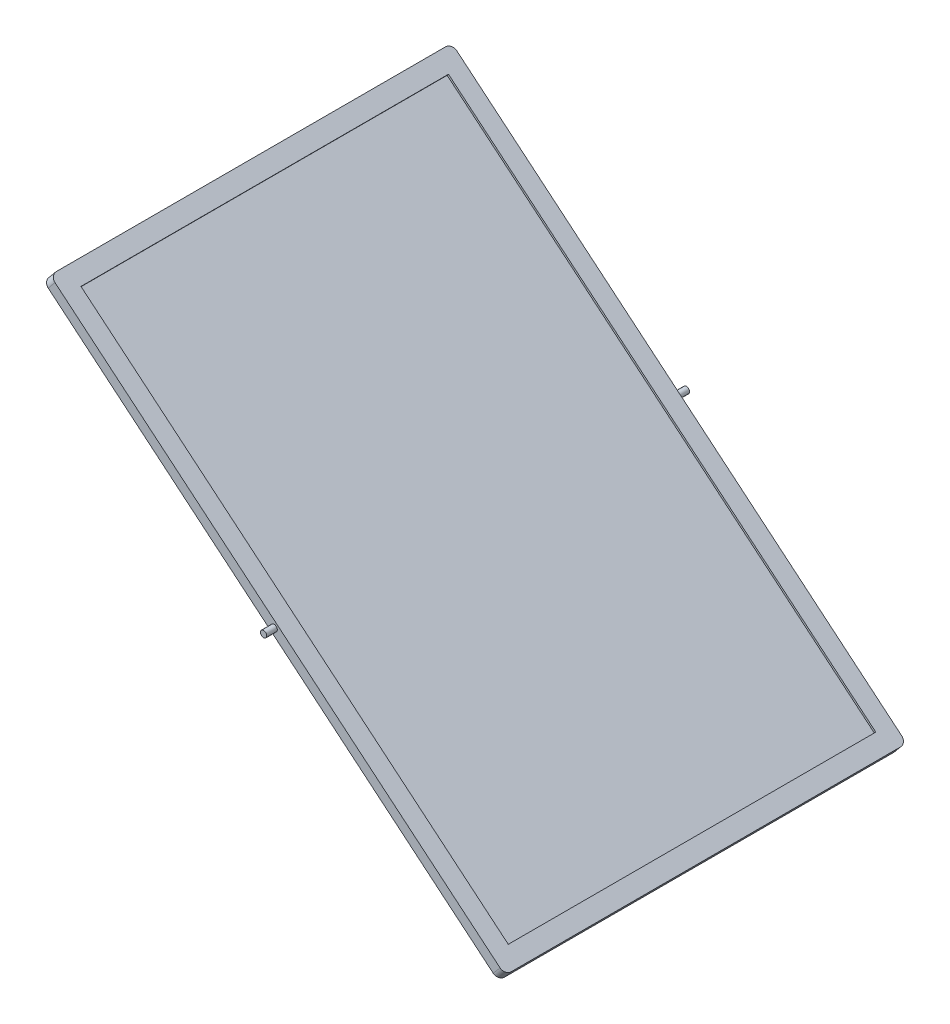
SolidWorks part; units mm, degrees
ref_plane "Front" through (0, 0, 0) normal (0, 0, 1) x (1, 0, 0)
ref_plane "Top" through (0, 0, 0) normal (0, 1, 0) x (1, 0, 0)
ref_plane "Right" through (0, 0, 0) normal (1, 0, 0) x (0, 0, -1)
sketch "草图1" plane through (0, 0, 0) normal (0, 0, 1) x (1, 0, 0)
  line L0 (-7.852, 22.5836) -> (-11.0529, 18.7425)
  line L1 (-11.0529, 18.7425) -> (204.049, -160.5092)
  line L2 (204.049, -160.5092) -> (207.25, -156.6681)
  line L3 (207.25, -156.6681) -> (-7.852, 22.5836)
  dimension "D1" = 5
  dimension "D2" = 280
extrude "凸台-拉伸1" add sketch "草图1" along normal blind 190
fillet "圆角1" radius 3 1 edges at (205.6495, -158.5886, 0)
fillet "圆角2" radius 3 1 edges at (205.6495, -158.5886, 190)
fillet "圆角3" radius 3 1 edges at (-9.4524, 20.663, 190)
fillet "圆角4" radius 3 1 edges at (-9.4524, 20.663, 0)
sketch "草图2" plane through (7.8887, 9.4664, 0) normal (0.6402, 0.7682, 0) x (0.7682, -0.6402, 0)
  line L0 (-43.7388, -95) -> (285.8015, -95) construction
  line L1 (-12.0278, -8.0871) -> (251.0484, -8.0871)
  line L2 (-12.0278, -8.0871) -> (-12.0278, -181.9129)
  line L3 (-12.0278, -181.9129) -> (251.0484, -181.9129)
  line L4 (251.0484, -8.0871) -> (251.0484, -181.9129)
  line L5 (256.5103, 0) -> (-17.4897, 0) construction
  line L6 (256.5103, -190) -> (-17.4897, -190) construction
  line L7 (119.5103, 26.5158) -> (119.5103, -214.3222) construction
  line L8 (259.5103, -187) -> (259.5103, -3) construction
  line L9 (-20.4897, -187) -> (-20.4897, -3) construction
extrude "切除-拉伸1" cut sketch "草图2" against normal blind 1
sketch "草图3" plane through (0, 0, 0) normal (0, 0, -1) x (-1, 0, 0)
  line L4 (-80.4882, -90.0952) -> (-128.8367, -32.077) construction
  line L5 (13.3016, 23.8707) -> (-215.8703, -167.1059) construction
  line L6 (8.7482, 16.8219) -> (-201.7444, -158.5886) construction
  line L7 (-204.9453, -154.7475) -> (5.5473, 20.663) construction
  line L8 (8.7482, 16.8219) -> (5.5473, 20.663) construction
  line L9 (-204.9453, -154.7475) -> (-201.7444, -158.5886) construction
  circle A0 centre (-98.0985, -68.9628) radius 1.5
extrude "凸台-拉伸2" add sketch "草图3" along normal blind 5 contours A0
cosmetic thread "装饰螺纹线2" parameters "D2"=1
sketch "草图4" plane through (0, 0, 190) normal (0, 0, 1) x (1, 0, 0)
  line L0 (106.4273, -58.9683) -> (85.4631, -84.1253) construction
  line L1 (209.3501, -161.6724) -> (-23.9228, 32.7217) construction
  line L2 (204.9453, -154.7475) -> (-5.5473, 20.663) construction
  line L3 (-8.7482, 16.8219) -> (201.7444, -158.5886) construction
  line L4 (201.7444, -158.5886) -> (204.9453, -154.7475) construction
  line L5 (-5.5473, 20.663) -> (-8.7482, 16.8219) construction
  circle A0 centre (98.0985, -68.9628) radius 1.5
extrude "凸台-拉伸3" add sketch "草图4" along normal blind 5 contours A0
cosmetic thread "装饰螺纹线1" parameters "D2"=1
